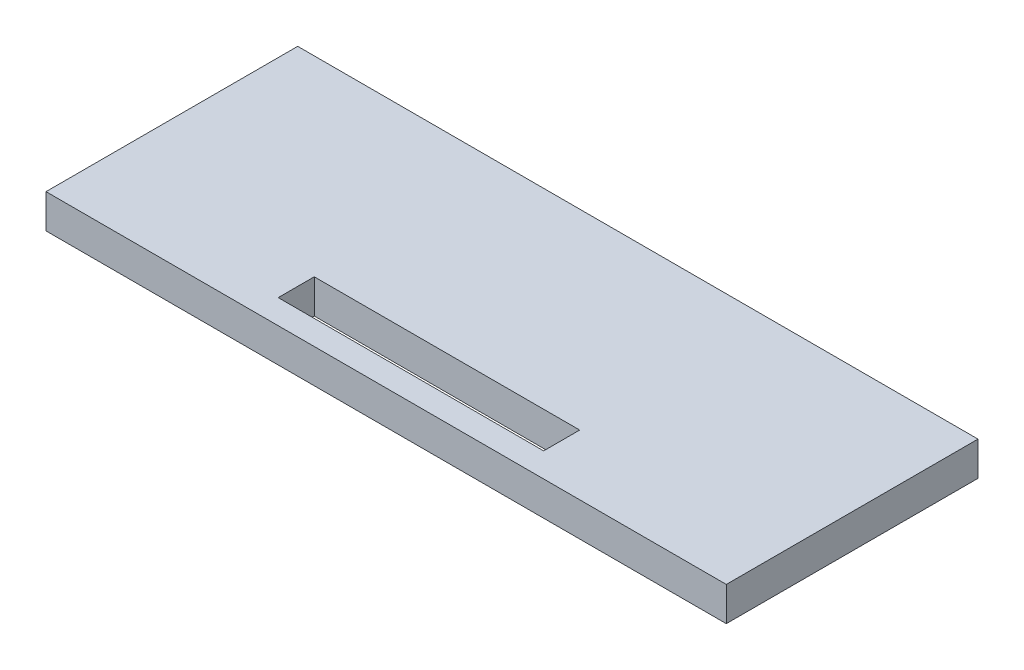
SolidWorks part; units mm, degrees
ref_plane "Alzado" through (0, 0, 0) normal (0, 0, 1) x (1, 0, 0)
ref_plane "Planta" through (0, 0, 0) normal (0, 1, 0) x (1, 0, 0)
ref_plane "Vista lateral" through (0, 0, 0) normal (1, 0, 0) x (0, 0, -1)
sketch "Croquis1" plane through (0, 0, 0) normal (0, 0, 1) x (1, 0, 0)
  line L0 (-50, 86.6025) -> (-50, 90.6025)
  line L1 (-50, 90.6025) -> (50, 90.6025)
  line L2 (30.3881, 90.6025) -> (52.3042, 90.6025) construction
  line L3 (50, 90.6025) -> (50, 86.6025)
  line L4 (50, 86.6025) -> (-50, 86.6025)
extrude "Saliente-Extruir1" add sketch "Croquis1" along normal up to surface (37 mm away)
sketch "Croquis2" plane through (0, 90.6025, 0) normal (0, 1, 0) x (1, 0, 0)
  line L4 (-50, 0) -> (-50, -37)
  line L5 (-50, -37) -> (50, -37)
  line L6 (50, -37) -> (50, 0)
  line L7 (50, 0) -> (-50, 0)
  line L8 (-50, 0) -> (-50, -37)
  line L9 (-50, -37) -> (50, -37)
  line L10 (50, -37) -> (50, 0)
  line L11 (50, 0) -> (-50, 0)
  dimension "D1" = 0
extrude "Saliente-Extruir2" add sketch "Croquis2" along normal blind 1
sketch "Croquis3" plane through (0, 91.6025, 0) normal (0, 1, 0) x (1, 0, 0)
  line L0 (0.066, -33.2244) -> (0.066, -33.4244)
  line L1 (-14.8835, -33.2244) -> (15.0154, -33.2244) construction
  line L2 (-19.4431, -33.4244) -> (19.575, -33.4244)
  line L3 (19.575, -33.4244) -> (19.575, -28.1244)
  line L4 (19.575, -28.1244) -> (0.028, -28.1244)
  line L5 (-19.4431, -28.1244) -> (0.1039, -28.1244)
  line L6 (-19.4431, -33.4244) -> (-19.4431, -28.1244)
extrude "Cortar-Extruir1" cut sketch "Croquis3" against normal blind 10 and the other way through all
